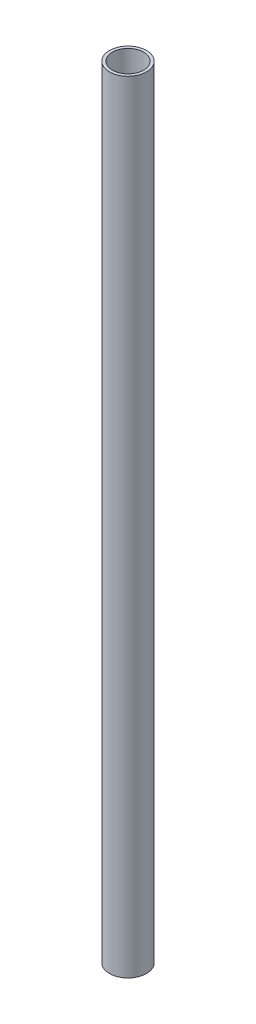
SolidWorks part; units mm, degrees
material "Hexcel AS4C (3000 Filaments)"
ref_plane "Front Plane" through (0, 0, 0) normal (0, 0, 1) x (1, 0, 0)
ref_plane "Top Plane" through (0, 0, 0) normal (0, 1, 0) x (1, 0, 0)
ref_plane "Right Plane" through (0, 0, 0) normal (1, 0, 0) x (0, 0, -1)
sketch "Sketch1" plane through (0, 0, 0) normal (0, 1, 0) x (1, 0, 0)
  circle A0 centre (0, 0) radius 4.75
  circle A1 centre (0, 0) radius 4
  dimension "D1" = 8
  dimension "D2" = 9.5
extrude "Boss-Extrude1" add sketch "Sketch1" along normal blind 200
